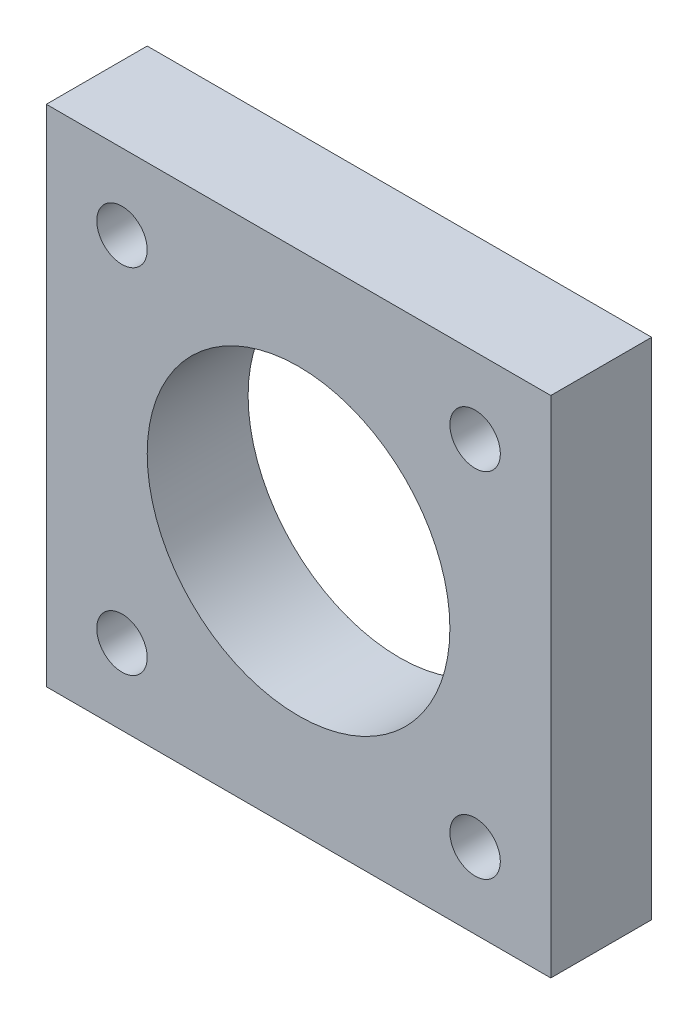
SolidWorks part; units mm, degrees
ref_plane "Front Plane" through (0, 0, 0) normal (0, 0, 1) x (1, 0, 0)
ref_plane "Top Plane" through (0, 0, 0) normal (0, 1, 0) x (1, 0, 0)
ref_plane "Right Plane" through (0, 0, 0) normal (1, 0, 0) x (0, 0, -1)
sketch "Sketch1" plane through (0, 0, 0) normal (0, 0, 1) x (1, 0, 0)
  circle A0 centre (0, 0) radius 15
  circle A1 centre (0, 0) radius 10
  dimension "D1" = 30
  dimension "D2" = 20
extrude "Boss-Extrude1" add sketch "Sketch1" along normal blind 30
sketch "Sketch2" plane through (0, 0, 0) normal (0, 0, -1) x (-1, 0, 0)
  line L1 (-25, 25) -> (25, 25)
  line L2 (-25, 25) -> (-25, -25)
  line L3 (-25, -25) -> (25, -25)
  line L4 (25, 25) -> (25, -25)
  line L5 (-25, 25) -> (25, -25) construction
  line L6 (-25, -25) -> (25, 25) construction
  point P0 (0, 0)
  dimension "D1" = 50
  dimension "D2" = 50
extrude "Boss-Extrude2" add sketch "Sketch2" along normal blind 10
sketch "Sketch3" plane through (0, 0, 0) normal (0, 0, 1) x (1, 0, 0)
  line L2 (0, 26.9354) -> (0, -27.4448) construction
  line L3 (-31.0107, 0) -> (35.0224, 0) construction
  line L4 (-25, 25) -> (25, 25) construction
  line L5 (-25, -25) -> (-25, 25) construction
  circle A0 centre (-17.5, 17.5) radius 2.5
  circle A1 centre (-17.5, -17.5) radius 2.5
  circle A2 centre (17.5, -17.5) radius 2.5
  circle A3 centre (17.5, 17.5) radius 2.5
  dimension "D1" = 5
  dimension "D2" = 35
  dimension "D3" = 35
  dimension "D6" = 7.5
  dimension "D7" = 7.5
  dimension "D4" = 2
  dimension "D5" = 2
extrude "Cut-Extrude1" cut sketch "Sketch3" against normal blind 10
sketch "Sketch4" plane through (0, 0, 0) normal (0, 0, 1) x (1, 0, 0)
  circle A0 centre (0, 0) radius 15
  circle A1 centre (0, 0) radius 10
extrude "Cut-Extrude2" cut sketch "Sketch4" along normal blind 30
sketch "Sketch5" plane through (0, 0, 0) normal (0, 0, 1) x (1, 0, 0)
  circle A0 centre (0, 0) radius 15
extrude "Cut-Extrude3" cut sketch "Sketch5" against normal blind 30
